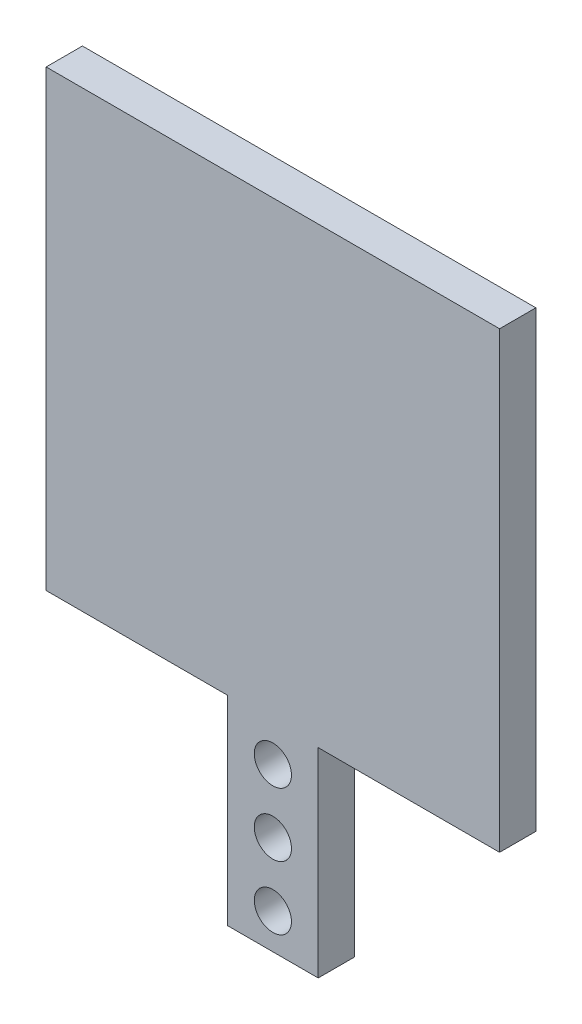
SolidWorks part; units mm, degrees
ref_plane "Front Plane" through (0, 0, 0) normal (0, 0, 1) x (1, 0, 0)
ref_plane "Top Plane" through (0, 0, 0) normal (0, 1, 0) x (1, 0, 0)
ref_plane "Right Plane" through (0, 0, 0) normal (1, 0, 0) x (0, 0, -1)
sketch "Sketch1" plane through (0, 0, 0) normal (0, 0, 1) x (1, 0, 0)
  line L0 (25, -22) -> (25, 0) construction
  line L1 (0, 0) -> (20, 0)
  line L2 (0, 0) -> (0, 50)
  line L3 (0, 50) -> (50, 50)
  line L4 (50, 0) -> (50, 50)
  line L6 (20, 0) -> (20, -22)
  line L7 (20, -22) -> (30, -22)
  line L8 (30, 0) -> (30, -22)
  line L9 (30, 0) -> (50, 0)
  circle A0 centre (25, -18.1) radius 2.05
  circle A1 centre (25, -11.1) radius 2.05
  circle A2 centre (25, -4.1) radius 2.05
  point P12 (25, 50)
  dimension "D5" = 4.1
  dimension "D6" = 4.1
  dimension "D7" = 4.1
  dimension "D8" = 3.9
  dimension "D9" = 7
  dimension "D10" = 7
  dimension "D1" = 50
  dimension "D2" = 50
  dimension "D3" = 22
  dimension "D4" = 10
extrude "Boss-Extrude1" add sketch "Sketch1" along normal blind 4
